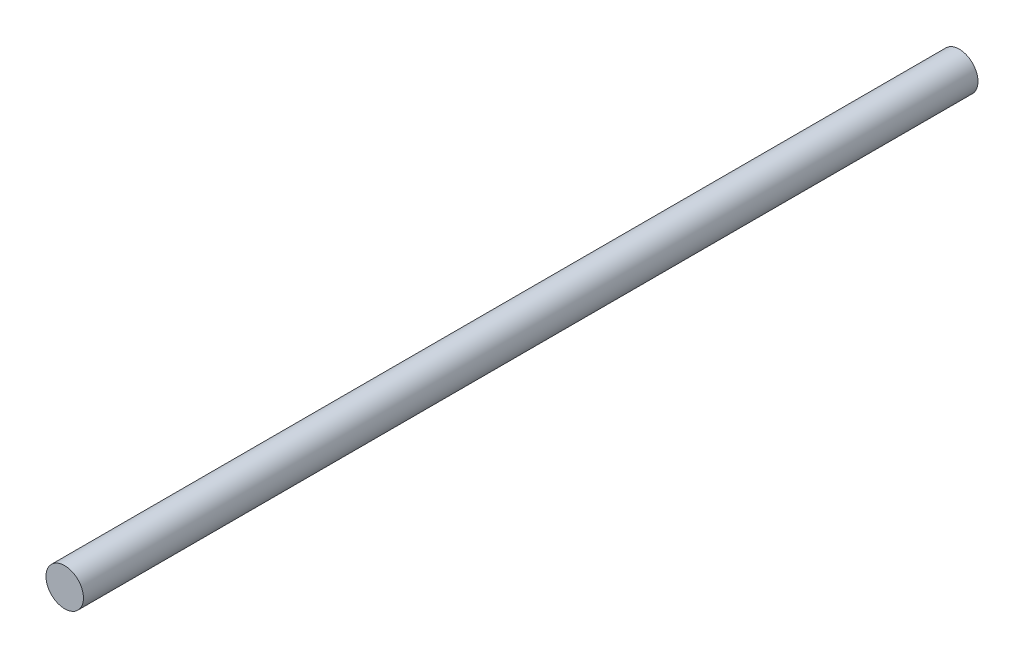
SolidWorks part; units mm, degrees
ref_plane "Front Plane" through (0, 0, 0) normal (0, 0, 1) x (1, 0, 0)
ref_plane "Top Plane" through (0, 0, 0) normal (0, 1, 0) x (1, 0, 0)
ref_plane "Right Plane" through (0, 0, 0) normal (1, 0, 0) x (0, 0, -1)
sketch "Sketch1" plane through (0, 0, 0) normal (0, 0, 1) x (1, 0, 0)
  circle A0 centre (0, 0) radius 8
  dimension "D1" = 16
extrude "Boss-Extrude1" add sketch "Sketch1" along normal mid plane 382
